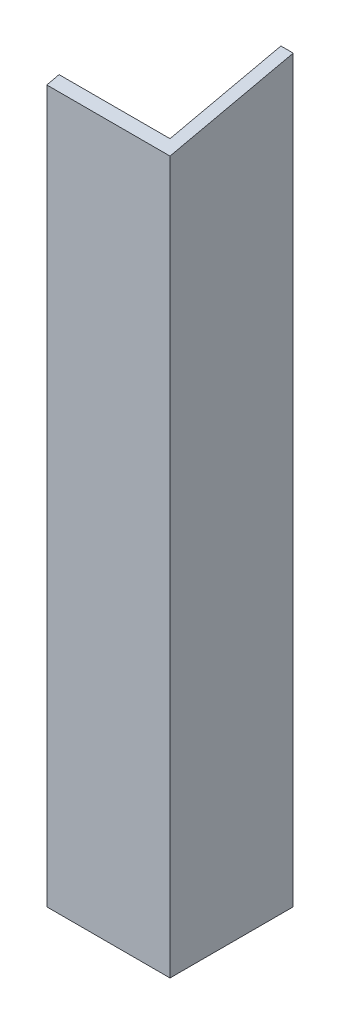
SolidWorks part; units mm, degrees
material "AISI 1020"
ref_plane "Front Plane" through (0, 0, 0) normal (0, 0, 1) x (1, 0, 0)
ref_plane "Top Plane" through (0, 0, 0) normal (0, 1, 0) x (1, 0, 0)
ref_plane "Right Plane" through (0, 0, 0) normal (1, 0, 0) x (0, 0, -1)
sketch "Sketch1" plane through (0, 0, 0) normal (0, 0, 1) x (1, 0, 0)
  line L1 (-3.2273, 4.2045) -> (16.7727, 4.2045)
  line L2 (-3.2273, 4.2045) -> (-3.2273, -115.7955)
  line L3 (-3.2273, -115.7955) -> (16.7727, -115.7955)
  line L4 (16.7727, 4.2045) -> (16.7727, -115.7955)
  dimension "D1" = 20
  dimension "D2" = 120
extrude "Boss-Extrude1" add sketch "Sketch1" against normal blind 20
sketch "Sketch4" plane through (-3.2273, 0, 0) normal (-1, 0, 0) x (0, 0, 1)
  line L0 (-20, 4.2045) -> (0, -0.266)
  line L1 (0, 4.2045) -> (0, -115.7955) construction
  line L2 (0, -0.266) -> (0, 4.2045)
  line L3 (0, 4.2045) -> (-20, 4.2045)
extrude "Cut-Extrude2" cut sketch "Sketch4" against normal blind 20
sketch "Sketch5" plane through (0, -115.7955, 0) normal (0, -1, 0) x (1, 0, 0)
  line L0 (16.7727, -20) -> (14.7727, -20)
  line L10 (-3.2273, -20) -> (16.7727, -20) construction
  line L15 (14.7727, -20) -> (14.7727, -2)
  line L17 (14.7727, -2) -> (-3.2273, -2)
  line L18 (14.7727, -2) -> (14.7727, -20)
  line L19 (14.7727, -20) -> (-3.2273, -20)
  line L20 (-3.2273, -2) -> (-3.2273, -20)
  line M4 (-3.2273, 0) -> (-3.2273, -20)
  line M5 (-3.2273, -20) -> (16.7727, -20)
  dimension "D1" = 2
  dimension "D2" = 18
extrude "Cut-Extrude4" cut sketch "Sketch5" against normal blind 120 contours L15 L17 M4 M5
